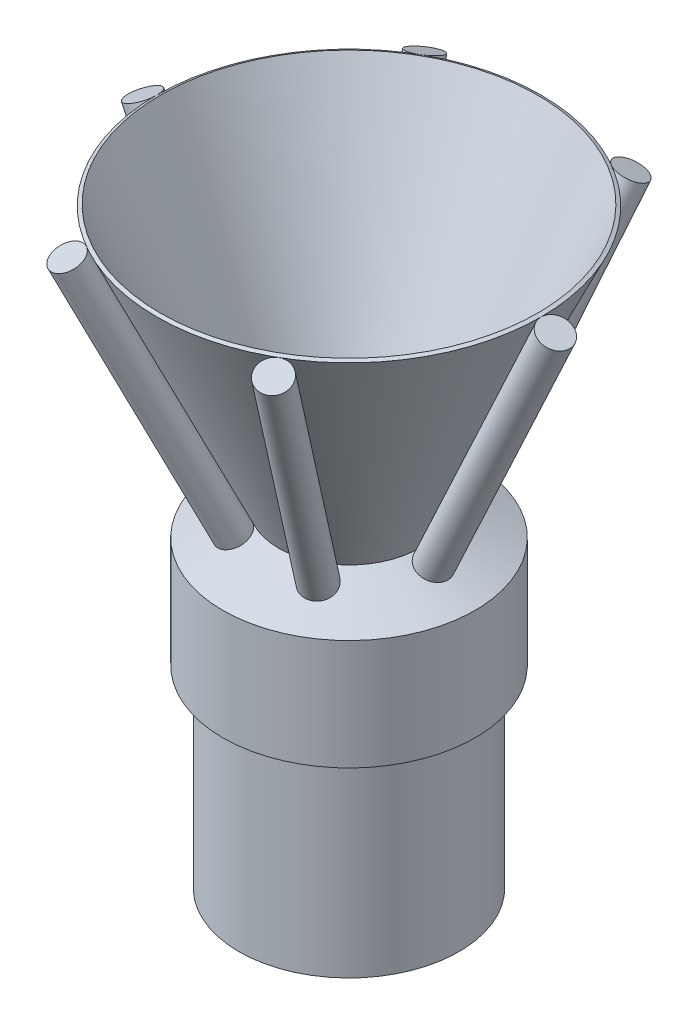
SolidWorks part; units mm, degrees
ref_plane "Front Plane" through (0, 0, 0) normal (0, 0, 1) x (1, 0, 0)
ref_plane "Top Plane" through (0, 0, 0) normal (0, 1, 0) x (1, 0, 0)
ref_plane "Right Plane" through (0, 0, 0) normal (1, 0, 0) x (0, 0, -1)
sketch "Sketch1" plane through (0, 0, 0) normal (0, 1, 0) x (1, 0, 0)
  circle A0 centre (0, 0) radius 75
  circle A1 centre (0, 0) radius 175
  dimension "D1" = 150
  dimension "D2" = 100
extrude "Boss-Extrude1" add sketch "Sketch1" along normal blind 457
sketch "Sketch2" plane through (0, 0, 0) normal (0, 0, 1) x (1, 0, 0)
  line L0 (0, 0) -> (0, 600.1152) construction
  line L1 (-175, 307) -> (-200.4, 307)
  line L2 (-175, 457) -> (-175, 0) construction
  line L3 (-200.4, 307) -> (-200.4, 482.4)
  line L4 (-200.4, 482.4) -> (-107.1258, 525.8945)
  line L9 (-107.1258, 525.8945) -> (-75, 457)
  line L10 (75, 457) -> (-75, 457) construction
  line L11 (-75, 457) -> (-175, 457)
  line L12 (-175, 457) -> (-175, 307)
  point P7 (-175, 514.5665)
  point P9 (-107.2037, 526.0611)
  point P10 (-108.3651, 525.8944)
  point P19 (-144.4173, 524.3632)
  point P20 (-103.7205, 537.2327)
  dimension "D1" = 75
  dimension "D2" = 25.4
  dimension "D3" = 25
  dimension "D4" = 25
  dimension "D7" = 150
  dimension "D8" = 25.4
revolve "Revolve1" add sketch "Sketch2" angle 360 about L0
ref_plane "Plane1" through (220.5626, 472.998, 0) normal (0.4226, 0.9063, 0) x (0.9063, -0.4226, 0)
ref_axis "Axis1" through (0, 457, 0) along (0, -1, 0)
sketch "Sketch3" plane through (220.5626, 472.998, 0) normal (0.4226, 0.9063, 0) x (0.9063, -0.4226, 0)
  line L0 (0, 0) -> (-304.3003, 0) construction
  circle A0 centre (-95, 0) radius 25
  point P5 (0, 0)
  dimension "D1" = 50
  dimension "D2" = 95
extrude "Cut-Extrude1" cut sketch "Sketch3" against normal blind 50
pattern_circular "CirPattern1" count 6 over 360 about axis through (0, 0, 0) along (0, 1, 0) of "Cut-Extrude1"
sketch "Sketch4" plane through (-199.4317, 427.6826, 0) normal (-0.4226, 0.9063, 0) x (0.9063, 0.4226, 0)
  circle A0 centre (95, 0) radius 25
extrude "Boss-Extrude2" add sketch "Sketch4" along normal blind 508
pattern_circular "CirPattern2" count 6 over 360 about axis through (0, 0, 0) along (0, 1, 0) of "Boss-Extrude2"
sketch "Sketch7" plane through (0, 0, 0) normal (0, 0, 1) x (1, 0, 0)
  line L0 (-111.8057, 523.7122) -> (-305.3648, 938.8012)
  line L2 (-305.3648, 938.8012) -> (-299.927, 941.3369)
  line L3 (-299.927, 941.3369) -> (-106.4152, 526.3496)
  line L4 (-106.4152, 526.3496) -> (-111.8057, 523.7122)
  line L5 (0, 0) -> (0, 615.4462) construction
  line L6 (0, 482.4) -> (0, 525.8945) construction
  line L7 (0, 457) -> (0, 0) construction
  line L8 (-111.8057, 523.7122) -> (-305.3648, 938.8012) construction
  line L10 (-107.1258, 525.8945) -> (-111.8058, 523.7122) construction
  point P2 (-111.5263, 523.8425)
  point P5 (-107.1258, 525.8945)
  point P7 (-106.7395, 525.8945)
  point P8 (-106.5971, 525.8945)
  point P10 (-106.3491, 526.2079)
  point P18 (-111.8006, 523.7146)
  point P20 (0, 0)
  point P22 (-111.8057, 523.7122)
  point P24 (-305.3533, 938.7766)
  point P25 (-109.0483, 525.8945)
  point P26 (-106.9399, 525.8945)
  point P28 (-106.4152, 526.3496)
  dimension "D1" = 6
revolve "Revolve2" add sketch "Sketch7" angle 360 about axis through (0, 457, 0) along (0, -1, 0)
